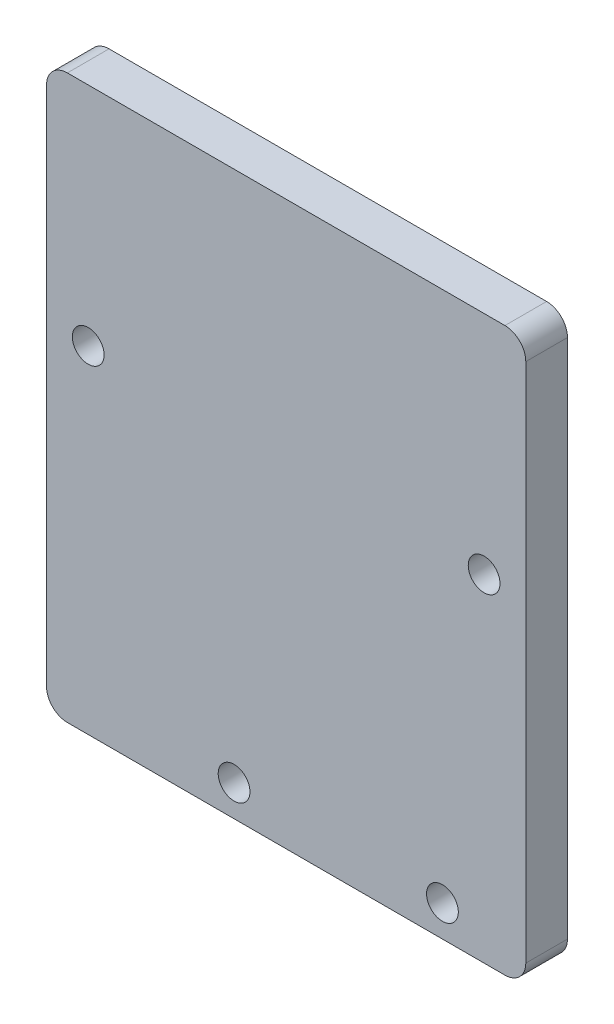
SolidWorks part; units mm, degrees
material "Thornel Mat VMA"
ref_plane "前视基准面" through (0, 0, 0) normal (0, 0, 1) x (1, 0, 0)
ref_plane "上视基准面" through (0, 0, 0) normal (0, 1, 0) x (1, 0, 0)
ref_plane "右视基准面" through (0, 0, 0) normal (1, 0, 0) x (0, 0, -1)
other "Configuration Table"
sketch "草图1" plane through (0, 0, 0) normal (0, 0, 1) x (1, 0, 0)
  line L1 (-23, -27) -> (23, -27)
  line L2 (-23, -27) -> (-23, 27)
  line L3 (-23, 27) -> (23, 27)
  line L4 (23, -27) -> (23, 27)
  line L5 (-23, -27) -> (23, 27) construction
  line L6 (-23, 27) -> (23, -27) construction
  point P0 (0, 0)
  dimension "D1" = 46
  dimension "D2" = 54
extrude "凸台-拉伸1" add sketch "草图1" along normal blind 4
sketch "草图2" plane through (0, 0, 4) normal (0, 0, 1) x (1, 0, 0)
  circle A0 centre (-5, -24) radius 1.5 construction
  circle A1 centre (15, -24) radius 1.5 construction
  circle A2 centre (-5, -24) radius 1.5
  circle A3 centre (15, -24) radius 1.5
sketch "草图3" plane through (0, 0, 0) normal (0, 0, -1) x (-1, 0, 0)
  circle A0 centre (19, 5.3103) radius 1.25 construction
  circle A1 centre (-19, 5.3103) radius 1.25 construction
  circle A2 centre (19, 5.3103) radius 1.25
  circle A3 centre (-19, 5.3103) radius 1.25
sketch "草图5" plane through (0, 0, 0) normal (0, 0, -1) x (-1, 0, 0)
  circle A0 centre (5, -24) radius 1.525
  circle A1 centre (-15, -24) radius 1.525
  circle A2 centre (-19, 5.3103) radius 1.525
  circle A3 centre (19, 5.3103) radius 1.525
  dimension "D1" = 3.05
extrude "切除-拉伸1" cut sketch "草图5" against normal blind 54
fillet "圆角1" radius 2 4 edges at (-23, 27, 2) (23, 27, 2) (23, -27, 2) (-23, -27, 2)
